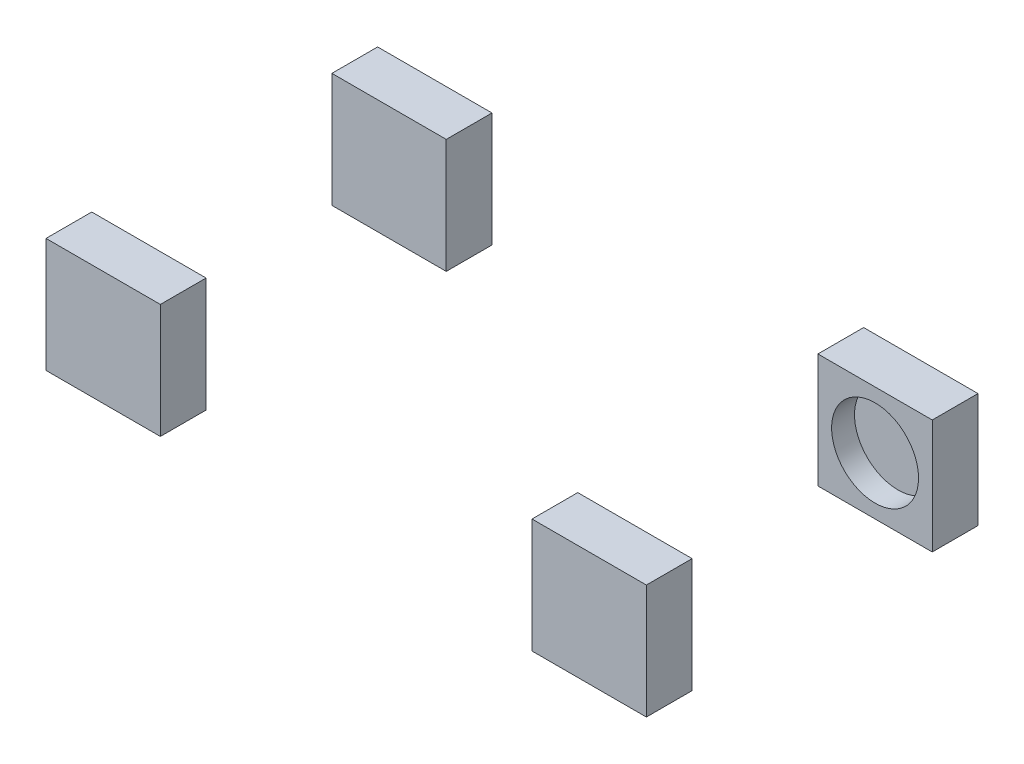
SolidWorks part; units mm, degrees
ref_plane "Front Plane" through (0, 0, 0) normal (0, 0, 1) x (1, 0, 0)
ref_plane "Top Plane" through (0, 0, 0) normal (0, 1, 0) x (1, 0, 0)
ref_plane "Right Plane" through (0, 0, 0) normal (1, 0, 0) x (0, 0, -1)
sketch "Sketch1" plane through (0, 0, 0) normal (0, 1, 0) x (1, 0, 0)
  line L0 (0, 175.6005) -> (0, -163.1385) construction
  line L1 (-212.5, -125) -> (212.5, -125)
  line L2 (-212.5, -125) -> (-212.5, 125)
  line L3 (-212.5, 125) -> (212.5, 125)
  line L4 (212.5, -125) -> (212.5, 125)
  line L5 (-212.5, -125) -> (212.5, 125) construction
  line L6 (-212.5, 125) -> (212.5, -125) construction
  line L7 (162.5, 105) -> (262.5, 105)
  line L8 (162.5, 105) -> (162.5, 145)
  line L9 (162.5, 145) -> (262.5, 145)
  line L10 (262.5, 105) -> (262.5, 145)
  line L11 (162.5, 105) -> (262.5, 145) construction
  line L12 (162.5, 145) -> (262.5, 105) construction
  line L13 (162.5, -105) -> (262.5, -105)
  line L14 (162.5, -105) -> (162.5, -145)
  line L15 (162.5, -145) -> (262.5, -145)
  line L16 (262.5, -105) -> (262.5, -145)
  line L17 (162.5, -105) -> (262.5, -145) construction
  line L18 (162.5, -145) -> (262.5, -105) construction
  line L19 (-231.0788, 0) -> (285.5483, 0) construction
  line L20 (-162.5, -145) -> (-262.5, -145)
  line L21 (-262.5, -105) -> (-262.5, -145)
  line L22 (-162.5, -105) -> (-262.5, -105)
  line L23 (-162.5, -105) -> (-162.5, -145)
  line L24 (-162.5, 145) -> (-262.5, 145)
  line L25 (-262.5, 105) -> (-262.5, 145)
  line L26 (-162.5, 105) -> (-262.5, 105)
  line L27 (-162.5, 105) -> (-162.5, 145)
  point P0 (0, 0)
  dimension "D1" = 425
  dimension "D2" = 250
  dimension "D3" = 100
  dimension "D4" = 40
  dimension "D5" = 40
  dimension "D6" = 100
extrude "Boss-Extrude1" add sketch "Sketch1" along normal mid plane 100 contours L3 L27 L24 L25 L26 L2 | L26 L27 L3 L2 | L7 L10 L9 L8 L3 L4 | L8 L7 L4 L3 | L16 L13 L4 L1 L14 L15 | L23 L1 L2 L22 L21 L20 | L23 L22 L2 L1
sketch "Sketch3" plane through (0, 0, 105) normal (0, 0, -1) x (-1, 0, 0)
  line L0 (-212.5, 50) -> (-212.5, -50) construction
  line L1 (-162.5, 50) -> (-262.5, 50) construction
  line L2 (-162.5, -50) -> (-262.5, -50) construction
  line L3 (-262.5, 0) -> (-162.5, 0) construction
  line L4 (-262.5, 50) -> (-262.5, -50) construction
  line L5 (-162.5, 50) -> (-162.5, -50) construction
  circle A0 centre (-212.5, 0) radius 38
  dimension "D1" = 76
extrude "Cut-Extrude5" cut sketch "Sketch3" against normal blind 20
sketch "Sketch4" plane through (0, 0, -105) normal (0, 0, 1) x (1, 0, 0)
  circle A0 centre (212.5, 0) radius 38 construction
  circle A1 centre (212.5, 0) radius 38
extrude "Cut-Extrude6" cut sketch "Sketch4" against normal blind 20
sketch3d "3DSketch4" plane through (0, 0, 0) normal (0, 0, 1) x (1, 0, 0)
  dimension "D1" = 8.42
sketch "Sketch5" plane through (0, 0, 116.58) normal (0, 0, -1) x (-1, 0, 0)
  line L0 (-212.5, 38) -> (-212.5, -50) construction
  line L1 (-250.5, 0) -> (-174.5, 0) construction
  line L2 (-162.5, -50) -> (-262.5, -50) construction
  line L3 (-162.5, -50) -> (-262.5, -50)
  line L4 (-208.5, -50) -> (-212.5, -27) construction
  line L5 (-212.5, -27) -> (-225.6719, 48.7387) construction
  line L6 (-162.5, 50) -> (-262.5, 50) construction
  line L7 (-162.5, 50) -> (-262.5, 50)
  circle A0 centre (-212.5, 0) radius 38 construction
  circle A1 centre (-212.5, 0) radius 38
  point P7 (-212.5, -27)
  point P15 (-221.8913, 27)
  dimension "D1" = 23
  dimension "D2" = 4
  dimension "D3" = 23
sketch3d "3DSketch5"
  line L0 (212.5, 38, 116.58) -> (212.5, -50, 116.58) construction
  line L1 (250.5, 0, 116.58) -> (174.5, 0, 116.58) construction
sketch "Sketch6" plane through (221.8913, 0, 0) normal (1, 0, 0) x (0, 0, -1)
  line L0 (-116.58, 27) -> (-110.904, 27) construction
  point P0 (-116.58, 27)
  point P5 (-110.904, 27)
  dimension "D1" = 5.676
sketch3d "3DSketch6"
  line L0 (221.8913, 27, 110.904) -> (212.5, -27, 116.58) construction
  point P0 (221.8913, 27, 110.904)
  point P2 (212.5, -27, 116.58)
sketch3d "3DSketch8" plane through (0, 0, 0) normal (0, 0, 1) x (1, 0, 0)
  dimension "D1" = 8.42
sketch "Sketch7" plane through (0, 0, -116.58) normal (0, 0, 1) x (1, 0, 0)
  line L0 (212.5, 50) -> (212.5, -50) construction
  line L1 (162.5, 50) -> (262.5, 50) construction
  line L2 (162.5, -50) -> (262.5, -50) construction
  line L3 (162.5, 0) -> (262.5, 0) construction
  line L4 (162.5, 50) -> (162.5, -50) construction
  line L5 (262.5, 50) -> (262.5, -50) construction
  line L6 (221.8913, 27) -> (212.5, -27) construction
  line L7 (221.8913, 27) -> (212.5, -27) construction
  point P12 (212.5, -27)
  point P13 (221.8913, 27)
sketch3d "3DSketch9"
  line L0 (212.5, 50, -116.58) -> (212.5, -50, -116.58) construction
  line L1 (162.5, 0, -116.58) -> (262.5, 0, -116.58) construction
sketch "Sketch8" plane through (221.8913, 0, 0) normal (-1, 0, 0) x (0, 0, 1)
  line L0 (-116.58, 27) -> (-110.91, 27) construction
  point P0 (-116.58, 27)
  point P5 (-110.91, 27)
  dimension "D1" = 5.67
sketch3d "3DSketch10"
  line L0 (221.8913, 27, -110.91) -> (212.5, -27, -116.58) construction
sketch3d "3DSketch11"
  line L0 (221.8913, 27, -116.58) -> (221.8913, 27, -110.91) construction
  line L1 (212.5, 50, -105) -> (212.5, -50, -105) construction
  line L2 (162.5, 50, -105) -> (262.5, 50, -105) construction
  line L3 (162.5, -50, -105) -> (262.5, -50, -105) construction
sketch "Sketch9" plane through (212.5, 0, 0) normal (-1, 0, 0) x (0, 0, 1)
  line L0 (-110.91, 27) -> (-89.7206, 27) construction
  line L1 (-110.91, 27) -> (285.7, -26.9974) construction
  line L2 (110.904, 27) -> (85.1327, 27) construction
  line L3 (110.904, 27) -> (-285.706, -26.9974) construction
  line L4 (-125, 50) -> (-125, -50) construction
  line L5 (-105, 50) -> (-145, 50) construction
  line L6 (-105, -50) -> (-145, -50) construction
  line L7 (125, 50) -> (125, -50) construction
  line L8 (105, 50) -> (145, 50) construction
  line L9 (105, -50) -> (145, -50) construction
  line L10 (-285.706, -26.9974) -> (285.7, -26.9974) construction
  line L11 (-125, -50) -> (285.7, -26.9974) construction
  line L12 (-285.706, -26.9974) -> (125, -50) construction
  line L13 (0, 78.2039) -> (0, -138.8888) construction
  point P20 (-116.58, -27)
  point P21 (116.58, -27)
  point P29 (0, -42.999)
  dimension "D1" = 7.753
  dimension "D2" = 396.61
  dimension "D3" = 7.753
  dimension "D4" = 396.61
  dimension "D5" = 7.001
  dimension "D6" = 410.706
sketch3d "3DSketch12" plane through (0, 0, 0) normal (0, 0, 1) x (1, 0, 0)
  dimension "D1" = 20
sketch "Sketch11" plane through (0, 0, -125) normal (0, 0, -1) x (-1, 0, 0)
  line L0 (162.5, -50) -> (262.5, -50) construction
  line L1 (162.5, 50) -> (262.5, 50) construction
  line L2 (162.5, -50) -> (262.5, -50)
  line L3 (162.5, 50) -> (262.5, 50)
  line L4 (212.5, 50) -> (212.5, -50) construction
  line L5 (162.5, 0) -> (262.5, 0) construction
  line L6 (162.5, 50) -> (162.5, -50) construction
  line L7 (262.5, 50) -> (262.5, -50) construction
  line L8 (-212.5, 50) -> (-212.5, -50) construction
  line L9 (-212.5, 50) -> (-212.5, -50) construction
  line L10 (-393.1005, -27) -> (329.5904, -27) construction
  line L11 (-221.8913, 27) -> (400.1441, -57.6885) construction
  line L12 (-221.8913, 27) -> (-156.9239, 27) construction
  line L13 (212.5, 27) -> (-336.1216, -104.3782) construction
  line L14 (212.5, 27) -> (147.1014, 27) construction
  line L15 (-212.5, -50) -> (174.7378, -27) construction
  line L16 (-12.9983, -27) -> (212.5, -50) construction
  point P12 (212.5, 27)
  point P13 (212.5, -27)
  point P14 (-212.5, -27)
  point P18 (56.0921, -34.047)
  point P27 (-12.9983, -27)
  point P29 (174.7378, -27)
  point P33 (-221.8913, 27)
  dimension "D1" = 23
  dimension "D2" = 54
  dimension "D3" = 7.753
  dimension "D4" = 13.467
  dimension "D5" = 225.4983
  dimension "D6" = 387.2378
  dimension "D7" = 15.953
  dimension "D8" = 268.5921
sketch3d "3DSketch13" plane through (0, 0, 0) normal (0, 0, 1) x (1, 0, 0)
  dimension "D1" = 20
sketch "Sketch12" plane through (0, 0, 125) normal (0, 0, -1) x (-1, 0, 0)
  line L0 (212.5, 50) -> (212.5, -50) construction
  line L1 (-221.8913, 27) -> (309.2663, -45.3157) construction
  line L2 (-221.8913, 27) -> (-150.1998, 27) construction
  line L3 (212.5, 27) -> (-290.0341, -93.3417) construction
  line L4 (162.5, -50) -> (262.5, -50)
  line L5 (262.5, -50) -> (262.5, 50)
  line L6 (262.5, 50) -> (162.5, 50)
  line L7 (162.5, 50) -> (162.5, -50)
  line L8 (162.5, -50) -> (262.5, -50)
  line L9 (262.5, -50) -> (262.5, 50)
  line L10 (262.5, 50) -> (162.5, 50)
  line L11 (162.5, 50) -> (162.5, -50)
  line L12 (212.5, 27) -> (139.4199, 27) construction
  line L13 (-212.5, -27) -> (212.5, -27) construction
  line L20 (-212.5, 50) -> (-212.5, -50) construction
  line L21 (-212.5, -50) -> (174.7378, -27) construction
  line L22 (212.5, -50) -> (-12.9983, -27) construction
  point P6 (212.5, -27)
  point P7 (212.5, 27)
  point P8 (-221.8913, 27)
  point P10 (174.7378, -27)
  point P24 (56.0921, -34.047)
  point P29 (-12.9983, -27)
  dimension "D2" = 23
  dimension "D3" = 54
  dimension "D4" = 7.753
  dimension "D5" = 13.467
  dimension "D6" = 225.4983
  dimension "D7" = 387.2378
  dimension "D8" = 15.953
  dimension "D1" = 0
sketch3d "3DSketch14" plane through (0, 0, 0) normal (0, 0, 1) x (1, 0, 0)
  dimension "D1" = 50
sketch "Sketch13" plane through (-212.5, 0, 0) normal (1, 0, 0) x (0, 0, -1)
  line L0 (-125, 50) -> (-125, -50) construction
  line L1 (-105, 50) -> (-145, 50) construction
  line L2 (-105, -50) -> (-145, -50) construction
  line L3 (125, 50) -> (125, -50) construction
  line L4 (105, 50) -> (145, 50) construction
  line L5 (105, -50) -> (145, -50) construction
  line L6 (0, 69.5621) -> (0, -61.9838) construction
  line L7 (-193.1722, -27) -> (206.3811, -27) construction
  line L8 (-110.91, 27) -> (114.5883, -27) construction
  line L9 (-110.91, 27) -> (-74.4999, 27) construction
  line L10 (110.91, 27) -> (79.0484, 27) construction
  line L11 (110.91, 27) -> (-114.5883, -27) construction
  line L12 (-125, -50) -> (114.5883, -27) construction
  line L13 (-114.5883, -27) -> (125, -50) construction
  point P12 (-110.91, 27)
  point P13 (-110.91, -27)
  point P17 (110.91, -27)
  point P18 (110.91, 27)
  point P26 (0, -38.0002)
  point P28 (114.5883, -27)
  point P30 (-114.5883, -27)
  dimension "D1" = 23
  dimension "D2" = 14.09
  dimension "D3" = 54
  dimension "D4" = 13.467
  dimension "D5" = 13.467
  dimension "D6" = 239.5883
  dimension "D7" = 11.9998
